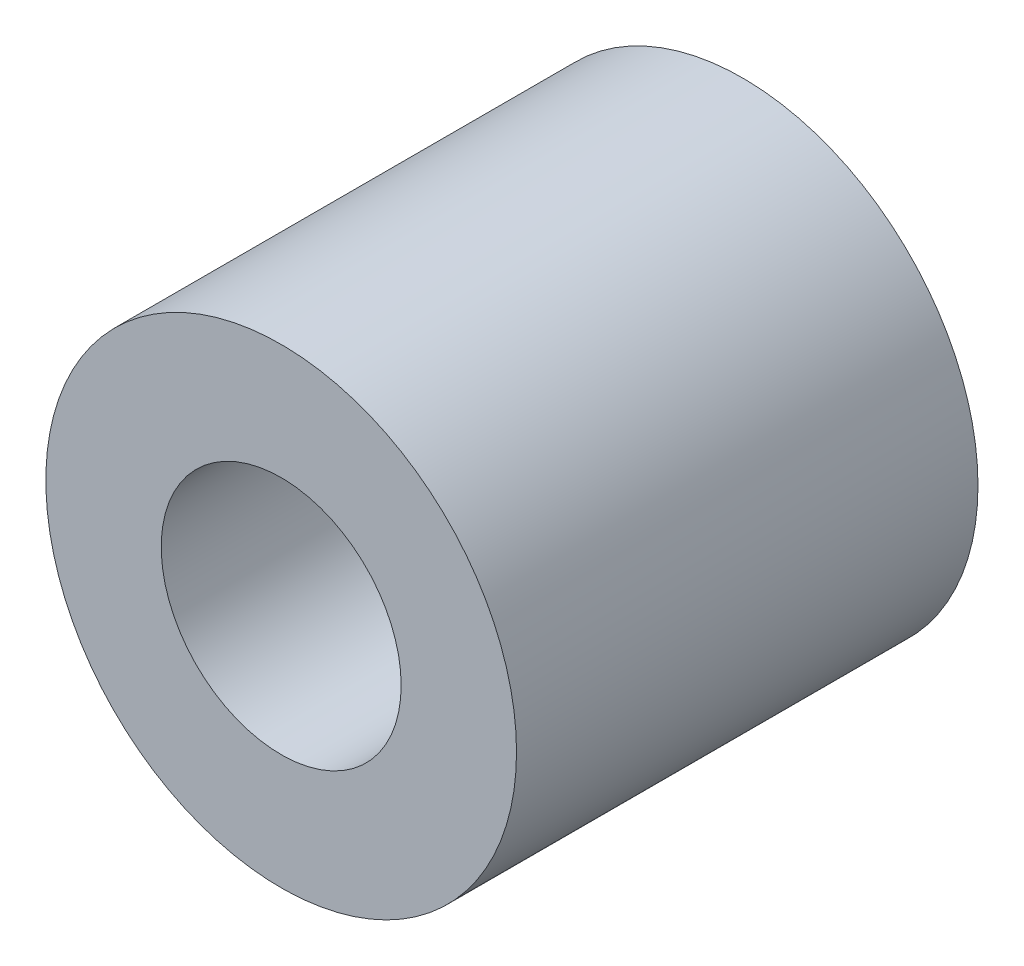
SolidWorks part; units mm, degrees
ref_plane "Alzado" through (0, 0, 0) normal (0, 0, 1) x (1, 0, 0)
ref_plane "Planta" through (0, 0, 0) normal (0, 1, 0) x (1, 0, 0)
ref_plane "Vista lateral" through (0, 0, 0) normal (1, 0, 0) x (0, 0, -1)
sketch "Croquis1" plane through (0, 0, 0) normal (0, 0, 1) x (1, 0, 0)
  circle A0 centre (0, 0) radius 2.6
  circle A1 centre (0, 0) radius 5.1
  dimension "D1" = 5.2
  dimension "D2" = 10.2
extrude "Saliente-Extruir1" add sketch "Croquis1" along normal blind 10
